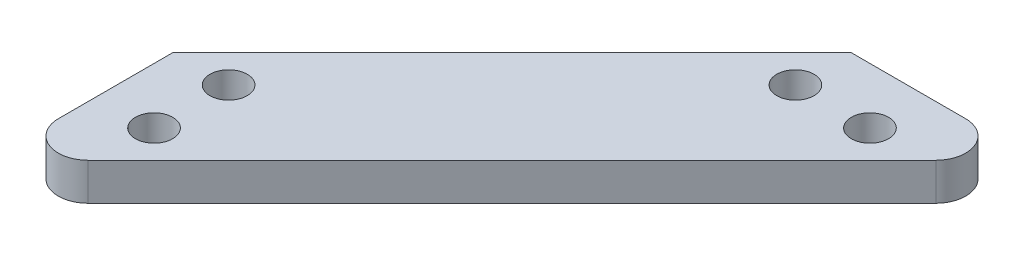
SolidWorks part; units mm, degrees
ref_plane "Front Plane" through (0, 0, 0) normal (0, 0, 1) x (1, 0, 0)
ref_plane "Top Plane" through (0, 0, 0) normal (0, 1, 0) x (1, 0, 0)
ref_plane "Right Plane" through (0, 0, 0) normal (1, 0, 0) x (0, 0, -1)
sketch "Sketch1" plane through (0, 0, 0) normal (0, 1, 0) x (1, 0, 0)
  line L0 (0, 0) -> (9.525, 0) construction
  line L1 (0, 0) -> (-9.525, 0) construction
  line L2 (-9.525, 0) -> (-9.6901, -14.4526) construction
  line L3 (-9.6901, -14.4526) -> (-9.6901, -20.8026) construction
  line L4 (-9.6901, -14.4526) -> (-14.4526, -14.4526) construction
  line L5 (-14.4526, -14.4526) -> (14.4526, 14.4526)
  line L7 (-14.4526, -14.4526) -> (-14.4526, -24.1955)
  line L11 (0, 0) -> (7.9375, -7.9375) construction
  line L12 (-10.1165, -25.9915) -> (25.9915, 10.1165)
  line L13 (14.4526, 14.4526) -> (24.1955, 14.4526)
  circle A0 centre (-9.6901, -14.4526) radius 1.5875
  circle A1 centre (-9.6901, -20.8026) radius 1.5875
  circle A2 centre (20.8026, 9.6901) radius 1.5875
  circle A3 centre (14.4526, 9.6901) radius 1.5875
  arc A4 (24.1955, 14.4526) -> (25.9915, 10.1165) centre (24.1955, 11.9126) cw
  arc A5 (-14.4526, -24.1955) -> (-10.1165, -25.9915) centre (-11.9126, -24.1955) ccw
  point P17 (0, 0)
  point P20 (30.3276, 14.4526)
  point P23 (-14.4526, -30.3276)
  dimension "D1" = 2.54
extrude "Boss-Extrude1" add sketch "Sketch1" along normal blind 3.175
